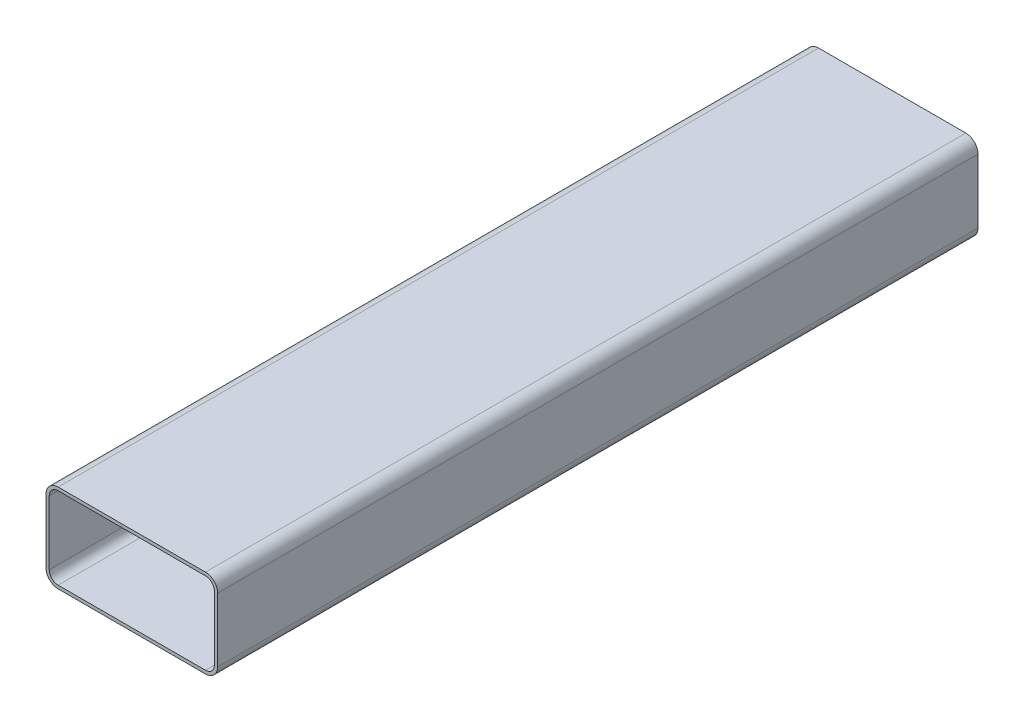
SolidWorks part; units mm, degrees
material "Zoltek Panex 33"
ref_plane "Front Plane" through (0, 0, 0) normal (0, 0, 1) x (1, 0, 0)
ref_plane "Top Plane" through (0, 0, 0) normal (0, 1, 0) x (1, 0, 0)
ref_plane "Right Plane" through (0, 0, 0) normal (1, 0, 0) x (0, 0, -1)
sketch "Sketch1" plane through (0, 0, 0) normal (0, 0, 1) x (1, 0, 0)
  line L1 (-49.2161, -27.305) -> (49.2161, -27.305)
  line L2 (-55.1561, -21.365) -> (-55.1561, 21.365)
  line L3 (-49.2161, 27.305) -> (49.2161, 27.305)
  line L4 (55.1561, -21.365) -> (55.1561, 21.365)
  line L5 (-55.1561, -27.305) -> (55.1561, 27.305) construction
  line L6 (-55.1561, 27.305) -> (55.1561, -27.305) construction
  line L7 (-49.2151, -29.464) -> (49.2151, -29.464)
  line L8 (-57.3151, -21.364) -> (-57.3151, 21.364)
  line L9 (-49.2151, 29.464) -> (49.2151, 29.464)
  line L10 (57.3151, -21.364) -> (57.3151, 21.364)
  line L11 (-57.3151, -29.464) -> (57.3151, 29.464) construction
  line L12 (-57.3151, 29.464) -> (57.3151, -29.464) construction
  arc A0 (49.2161, -27.305) -> (55.1561, -21.365) centre (49.2161, -21.365) ccw
  arc A1 (-49.2161, -27.305) -> (-55.1561, -21.365) centre (-49.2161, -21.365) cw
  arc A2 (-55.1561, 21.365) -> (-49.2161, 27.305) centre (-49.2161, 21.365) cw
  arc A3 (49.2161, 27.305) -> (55.1561, 21.365) centre (49.2161, 21.365) cw
  arc A4 (49.2151, -29.464) -> (57.3151, -21.364) centre (49.2151, -21.364) ccw
  arc A5 (-49.2151, -29.464) -> (-57.3151, -21.364) centre (-49.2151, -21.364) cw
  arc A6 (-57.3151, 21.364) -> (-49.2151, 29.464) centre (-49.2151, 21.364) cw
  arc A7 (49.2151, 29.464) -> (57.3151, 21.364) centre (49.2151, 21.364) cw
  point P0 (0, 0)
  point P18 (0, 0)
  dimension "D3" = 5.94
  dimension "D6" = 8.1
  dimension "D1" = 110.3122
  dimension "D2" = 54.61
  dimension "D4" = 2.159
  dimension "D5" = 2.159
extrude "Boss-Extrude1" add sketch "Sketch1" along normal blind 508
other "Freeze***"
